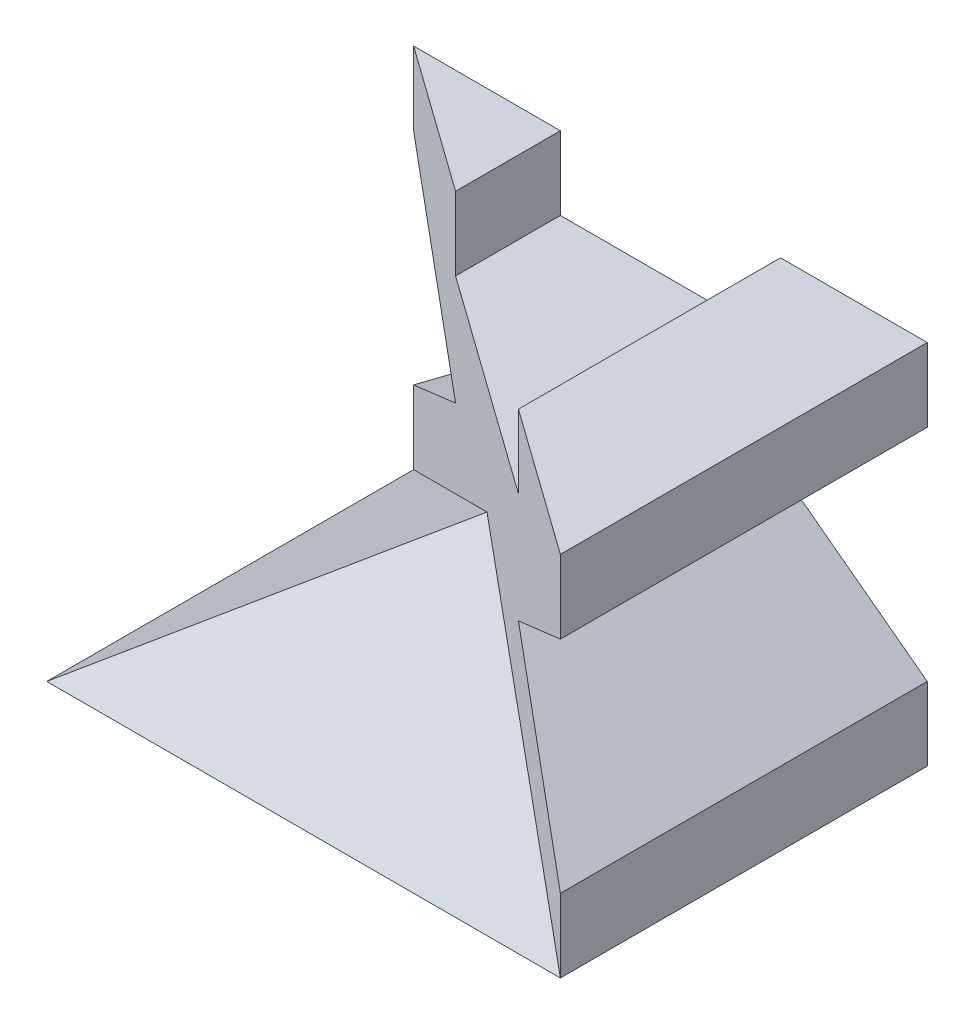
SolidWorks part; units mm, degrees
ref_plane "Front" through (0, 0, 0) normal (0, 0, 1) x (1, 0, 0)
ref_plane "Top" through (0, 0, 0) normal (0, 1, 0) x (1, 0, 0)
ref_plane "Right" through (0, 0, 0) normal (1, 0, 0) x (0, 0, -1)
sketch "Sketch1" plane through (0, 0, 0) normal (0, 0, 1) x (1, 0, 0)
  line L0 (0, 1.0456) -> (0, -0.9607) construction
  line L1 (-3.5, -2.5) -> (3.5, -2.5)
  line L2 (-3.5, -2.5) -> (-3.5, -1.5)
  line L3 (-3.5, 2.5) -> (-1.5, 2.5)
  line L4 (3.5, -2.5) -> (3.5, -1.5)
  line L5 (-3.5, -2.5) -> (3.5, 2.5) construction
  line L6 (-3.5, 2.5) -> (3.5, -2.5) construction
  line L7 (3.5, 1.5) -> (1.5, 0)
  line L8 (1.5, 0) -> (3.5, -1.5)
  line L10 (-3.5, 1.5) -> (-1.5, 0)
  line L11 (-1.5, 0) -> (-3.5, -1.5)
  line L12 (-0.6051, 0) -> (0.4671, 0) construction
  line L14 (-1.5, 2.5) -> (-1.5, 1.5)
  line L15 (-1.5, 1.5) -> (1.5, 1.5)
  line L16 (1.5, 2.5) -> (1.5, 1.5)
  line L20 (1.5, 2.5) -> (3.5, 2.5)
  line L21 (-3.5, 1.5) -> (-3.5, 2.5)
  line L22 (3.5, 1.5) -> (3.5, 2.5)
  point P0 (0, 0)
  dimension "D1" = 5
  dimension "D2" = 7
  dimension "D3" = 1
  dimension "D4" = 1
  dimension "D5" = 2
  dimension "D6" = 1.5
  dimension "D7" = 3
  dimension "D8" = 1
  dimension "D9" = 2
extrude "Boss-Extrude1" add sketch "Sketch1" along normal blind 5
sketch "Sketch2" plane through (0, 2.5, 0) normal (0, 1, 0) x (1, 0, 0)
  line L0 (-3.5, 0) -> (3.5, -5)
  line L1 (3.5, -5) -> (-3.5, -5)
  line L2 (-3.5, -5) -> (-3.5, 0)
extrude "Cut-Extrude1" cut sketch "Sketch2" against normal blind 5
sketch "Sketch3" plane through (0, -2.5, 0) normal (0, -1, 0) x (1, 0, 0)
  line L0 (-3.5, 0) -> (-3.5, 5)
  line L1 (-3.5, 5) -> (3.5, 5)
  line L2 (3.5, 5) -> (-3.5, 0)
extrude "Boss-Extrude2" add sketch "Sketch3" against normal blind 2.5
sketch3d "3DSketch2"
  line L0 (-3.5, -2.5, 0) -> (0, 0, 2.5)
  line L1 (-1.5, 0, 1.4286) -> (1.5, 0, 3.5714) construction
  line L2 (0, 0, 2.5) -> (-3.5, -2.5, 5)
  line L3 (-3.5, -2.5, 5) -> (-3.5, -2.5, 0)
extrude "Cut-Extrude2" cut sketch "3DSketch2" along direction (0, 1, 0) on the side of the normal blind 2.5
sketch3d "3DSketch3"
  line L0 (0, 0, 2.5) -> (-3.5, -2.5, 5)
  line L1 (-3.5, -2.5, 5) -> (3.5, -2.5, 5)
  line L2 (3.5, -2.5, 5) -> (0, 0, 2.5)
extrude "Cut-Extrude3" cut sketch "3DSketch3" along direction (0, 1, 0) on the side of the normal blind 2.5
